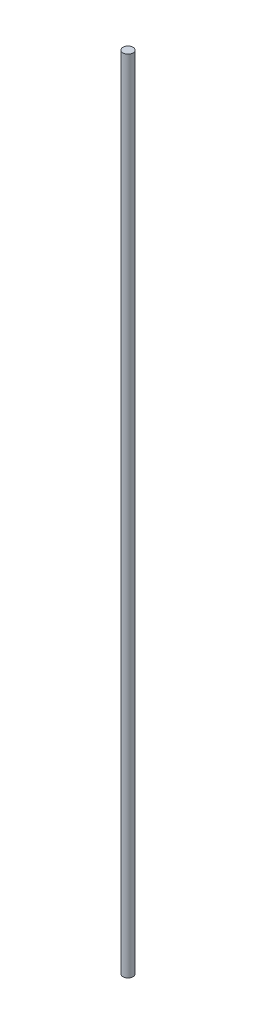
SolidWorks part; units mm, degrees
ref_plane "Front Plane" through (0, 0, 0) normal (0, 0, 1) x (1, 0, 0)
ref_plane "Top Plane" through (0, 0, 0) normal (0, 1, 0) x (1, 0, 0)
ref_plane "Right Plane" through (0, 0, 0) normal (1, 0, 0) x (0, 0, -1)
sketch "Sketch1" plane through (0, 0, 0) normal (0, 1, 0) x (1, 0, 0)
  circle A0 centre (0, 0) radius 1.5875
  dimension "D1" = 3.175
extrude "Boss-Extrude1" add sketch "Sketch1" along normal blind 254
